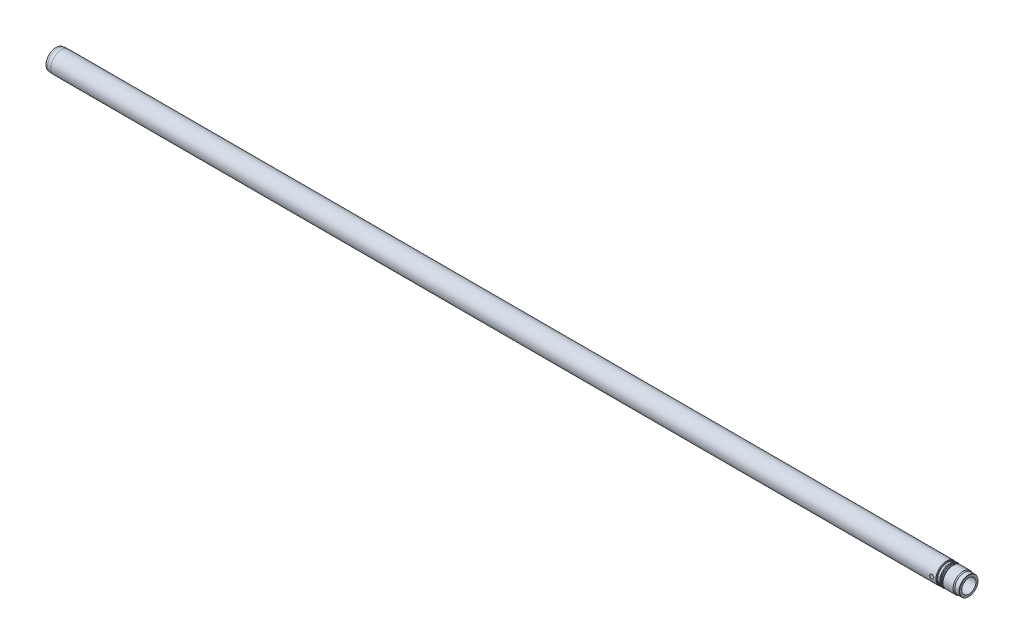
SolidWorks part; units mm, degrees
ref_plane "Front" through (0, 0, 0) normal (0, 0, 1) x (1, 0, 0)
ref_plane "Top" through (0, 0, 0) normal (0, 1, 0) x (1, 0, 0)
ref_plane "Right" through (0, 0, 0) normal (1, 0, 0) x (0, 0, -1)
sketch "Sketch1" plane through (0, 0, 0) normal (0, 0, 1) x (1, 0, 0)
  line L0 (0, 0) -> (2180, 0) construction
  line L1 (0, 21) -> (0, 23.5)
  line L2 (0.5, 24) -> (5, 24)
  line L3 (5, 24) -> (5, 24.75)
  line L4 (13, 25) -> (13, 24.75)
  line L5 (2180, 21.9226) -> (2179, 22.5)
  line L6 (5, 24.75) -> (13, 24.75)
  line L7 (2179, 22.5) -> (2169, 22.5)
  line L8 (13, 25) -> (2126.5, 25)
  line L9 (0, 21) -> (6.9282, 17)
  line L10 (6.9282, 17) -> (2180, 17)
  line L11 (2128, 24.134) -> (2128, 23.8)
  line L12 (2126.5, 25) -> (2128, 24.134)
  line L13 (2128.8, 23) -> (2133.2, 23)
  line L14 (2134, 23.8) -> (2134, 24.25)
  line L15 (2134.5, 24.75) -> (2135.5, 24.75)
  line L16 (2131, 23) -> (2131, 24) construction
  line L17 (2135.5, 24.75) -> (2137, 23.884)
  line L18 (2137, 23.884) -> (2137, 23.55)
  line L19 (2137.8, 22.75) -> (2140, 22.75)
  line L20 (2140, 22.75) -> (2142.4533, 24)
  line L21 (2142.4533, 24) -> (2166.4019, 24)
  line L22 (2180, 21.9226) -> (2180, 17)
  line L23 (0.5, 24) -> (0, 23.5)
  line L24 (2169, 22.5) -> (2166.4019, 24)
  arc A0 (2134, 24.25) -> (2134.5, 24.75) centre (2134.5, 24.25) cw
  arc A2 (2137, 23.55) -> (2137.8, 22.75) centre (2137.8, 23.55) ccw
  arc A3 (2128, 23.8) -> (2128.8, 23) centre (2128.8, 23.8) ccw
  arc A4 (2133.2, 23) -> (2134, 23.8) centre (2133.2, 23.8) ccw
  point P33 (2128, 23)
  point P36 (2134, 23)
  dimension "D7" = 30
  dimension "D16" = 0.8
  dimension "D22" = 0.8
  dimension "D31" = 49.5
  dimension "D33" = 0.5
  dimension "D3" = 5
  dimension "D4" = 48
  dimension "D5" = 1.5
  dimension "D6" = 46
  dimension "D8" = 13
  dimension "D9" = 34
  dimension "D10" = 30
  dimension "D11" = 42
  dimension "D12" = 48
  dimension "D13" = 45.5
  dimension "D14" = 27
  dimension "D15" = 30
  dimension "D17" = 6
  dimension "D18" = 43
  dimension "D19" = 3
  dimension "D20" = 46
  dimension "D21" = 2180
  dimension "D23" = 50
  dimension "D24" = 49.5
  dimension "D25" = 0.5
  dimension "D26" = 45
  dimension "D27" = 30
  dimension "D28" = 45
  dimension "D29" = 1
  dimension "D30" = 11
  dimension "D32" = 1.5
revolve "Base-Revolve" add sketch "Sketch1" angle 360 about L0
cosmetic thread "Cosmetic Thread1" parameters "D2"=45.835
sketch "Sketch2" plane through (0, 0, 0) normal (0, 0, 1) x (1, 0, 0)
  line L0 (0, 0) -> (2180, 0) construction
  line L3 (2180, -21.9226) -> (2180, 21.9226) construction
  circle A0 centre (2116, 0) radius 4.5
  dimension "D2" = 9
  dimension "D1" = 64
extrude "Cut-Extrude1" cut sketch "Sketch2" against normal mid plane 100
